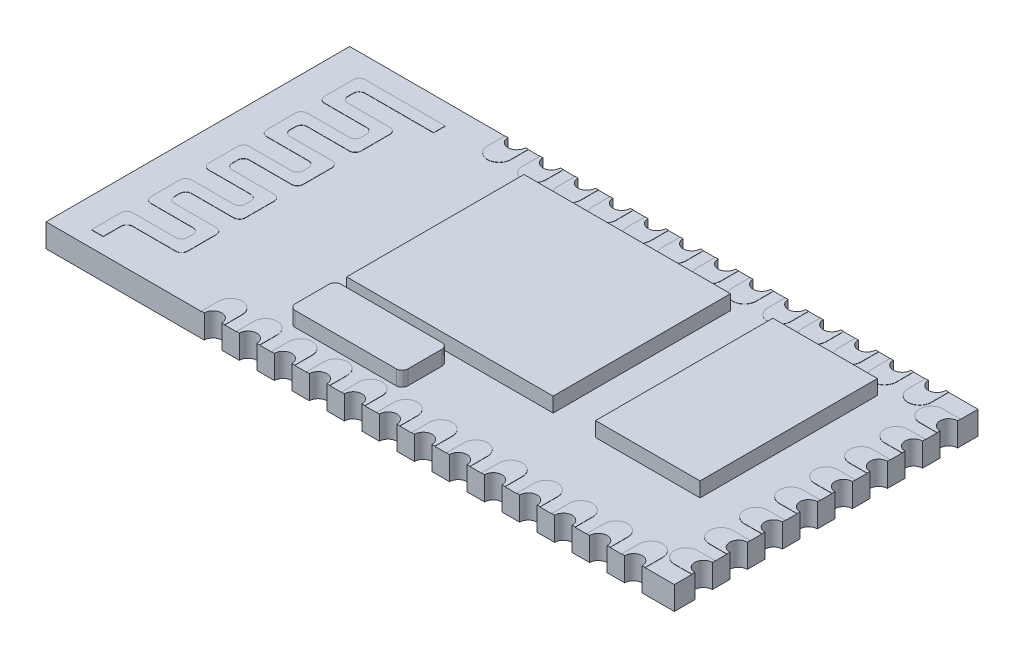
SolidWorks part; units mm, degrees
ref_plane "Front Plane" through (0, 0, 0) normal (0, 0, 1) x (1, 0, 0)
ref_plane "Top Plane" through (0, 0, 0) normal (0, 1, 0) x (1, 0, 0)
ref_plane "Right Plane" through (0, 0, 0) normal (1, 0, 0) x (0, 0, -1)
sketch "Sketch1" plane through (0, 0, 0) normal (0, 1, 0) x (1, 0, 0)
  line L1 (0, 0) -> (26.9, 0)
  line L2 (0, 0) -> (0, 13)
  line L3 (0, 13) -> (26.9, 13)
  line L4 (26.9, 0) -> (26.9, 13)
  dimension "D1" = 13
  dimension "D2" = 26.9
extrude "Boss-Extrude1" add sketch "Sketch1" along normal blind 1
sketch "Sketch2" plane through (0, 1, 0) normal (0, 1, 0) x (1, 0, 0)
  line L1 (24.2376, 11.3557) -> (19.7636, 11.3557)
  line L2 (24.2376, 11.3557) -> (24.2376, 3.7634)
  line L3 (24.2376, 3.7634) -> (19.7636, 3.7634)
  line L4 (19.7636, 11.3557) -> (19.7636, 3.7634)
  line L5 (9.1073, 11.3557) -> (17.9469, 11.3557)
  line L6 (9.1073, 11.3557) -> (9.1073, 3.7634)
  line L7 (9.1073, 3.7634) -> (17.9469, 3.7634)
  line L8 (17.9469, 11.3557) -> (17.9469, 3.7634)
extrude "Boss-Extrude2" add sketch "Sketch2" along normal blind 0.63
sketch "Sketch3" plane through (0, 1, 0) normal (0, 1, 0) x (1, 0, 0)
  line L0 (5.0017, 11.8414) -> (1.5699, 11.8414) construction
  line L1 (1.5699, 11.8414) -> (1.5699, 10.6027) construction
  line L2 (1.5699, 10.6027) -> (3.8747, 10.6027) construction
  line L3 (3.8747, 10.6027) -> (3.8747, 9.364) construction
  line L4 (3.8747, 9.364) -> (1.5699, 9.364) construction
  line L5 (1.5699, 9.364) -> (1.5699, 8.1252) construction
  line L6 (1.5699, 8.1252) -> (3.8747, 8.1252) construction
  line L7 (3.8747, 8.1252) -> (3.8747, 6.8865) construction
  line L8 (3.8747, 6.8865) -> (1.5699, 6.8865) construction
  line L9 (1.5699, 6.8865) -> (1.5699, 5.6478) construction
  line L10 (1.5699, 5.6478) -> (3.8747, 5.6478) construction
  line L11 (3.8747, 5.6478) -> (3.8747, 4.4091) construction
  line L12 (3.8747, 4.4091) -> (1.5699, 4.4091) construction
  line L13 (1.5699, 4.4091) -> (1.5699, 3.1704) construction
  line L14 (1.5699, 3.1704) -> (3.8747, 3.1704) construction
  line L15 (3.8747, 3.1704) -> (3.8747, 1.9317) construction
  line L16 (3.8747, 1.9317) -> (1.527, 1.9317) construction
  line L17 (1.527, 1.4451) -> (1.527, 0.1872) construction
  line L18 (5.0017, 12.0914) -> (1.5699, 12.0914)
  line L19 (1.3199, 11.8414) -> (1.3199, 10.6027)
  line L20 (1.5699, 10.3527) -> (3.3747, 10.3527)
  line L21 (3.6247, 10.1027) -> (3.6247, 9.864)
  line L22 (3.3747, 9.614) -> (1.5699, 9.614)
  line L23 (1.3199, 9.364) -> (1.3199, 8.1252)
  line L24 (1.5699, 7.8752) -> (3.3747, 7.8752)
  line L25 (3.6247, 7.6252) -> (3.6247, 7.3865)
  line L26 (3.3747, 7.1365) -> (1.5699, 7.1365)
  line L27 (1.3199, 6.8865) -> (1.3199, 5.6478)
  line L28 (1.5699, 5.3978) -> (3.3747, 5.3978)
  line L29 (3.6247, 5.1478) -> (3.6247, 4.9091)
  line L30 (3.3747, 4.6591) -> (1.5699, 4.6591)
  line L31 (1.3199, 4.4091) -> (1.3199, 3.1704)
  line L32 (1.5699, 2.9204) -> (3.3747, 2.9204)
  line L33 (3.6247, 2.6704) -> (3.6247, 2.4317)
  line L34 (3.3747, 2.1817) -> (1.527, 2.1817)
  line L35 (1.277, 1.9317) -> (1.277, 0.6739)
  line L36 (5.0017, 11.5914) -> (2.0699, 11.5914)
  line L37 (1.8199, 11.3414) -> (1.8199, 11.1027)
  line L38 (2.0699, 10.8527) -> (3.8747, 10.8527)
  line L39 (4.1247, 10.6027) -> (4.1247, 9.364)
  line L40 (3.8747, 9.114) -> (2.0699, 9.114)
  line L41 (1.8199, 8.864) -> (1.8199, 8.6252)
  line L42 (2.0699, 8.3752) -> (3.8747, 8.3752)
  line L43 (4.1247, 8.1252) -> (4.1247, 6.8865)
  line L44 (3.8747, 6.6365) -> (2.0699, 6.6365)
  line L45 (1.8199, 6.3865) -> (1.8199, 6.1478)
  line L46 (2.0699, 5.8978) -> (3.8747, 5.8978)
  line L47 (4.1247, 5.6478) -> (4.1247, 4.4091)
  line L48 (3.8747, 4.1591) -> (2.0699, 4.1591)
  line L49 (1.8199, 3.9091) -> (1.8199, 3.6704)
  line L50 (2.0699, 3.4204) -> (3.8747, 3.4204)
  line L51 (4.1247, 3.1704) -> (4.1247, 1.9317)
  line L52 (3.8747, 1.6817) -> (2.027, 1.6817)
  line L53 (1.777, 1.4317) -> (1.777, 0.6739)
  line L54 (5.0017, 12.0914) -> (5.0017, 11.5914)
  line L55 (1.777, 0.6739) -> (1.277, 0.6739)
  arc A0 (1.5699, 12.0914) -> (1.3199, 11.8414) centre (1.5699, 11.8414) ccw
  arc A1 (2.0699, 11.5914) -> (1.8199, 11.3414) centre (2.0699, 11.3414) ccw
  arc A2 (1.8199, 11.1027) -> (2.0699, 10.8527) centre (2.0699, 11.1027) ccw
  arc A3 (1.3199, 10.6027) -> (1.5699, 10.3527) centre (1.5699, 10.6027) ccw
  arc A4 (3.8747, 10.8527) -> (4.1247, 10.6027) centre (3.8747, 10.6027) cw
  arc A5 (3.3747, 10.3527) -> (3.6247, 10.1027) centre (3.3747, 10.1027) cw
  arc A6 (3.6247, 9.864) -> (3.3747, 9.614) centre (3.3747, 9.864) cw
  arc A7 (4.1247, 9.364) -> (3.8747, 9.114) centre (3.8747, 9.364) cw
  arc A8 (2.0699, 9.114) -> (1.8199, 8.864) centre (2.0699, 8.864) ccw
  arc A9 (1.5699, 9.614) -> (1.3199, 9.364) centre (1.5699, 9.364) ccw
  arc A10 (1.8199, 8.6252) -> (2.0699, 8.3752) centre (2.0699, 8.6252) ccw
  arc A11 (1.3199, 8.1252) -> (1.5699, 7.8752) centre (1.5699, 8.1252) ccw
  arc A12 (3.3747, 7.8752) -> (3.6247, 7.6252) centre (3.3747, 7.6252) cw
  arc A13 (3.8747, 8.3752) -> (4.1247, 8.1252) centre (3.8747, 8.1252) cw
  arc A14 (4.1247, 6.8865) -> (3.8747, 6.6365) centre (3.8747, 6.8865) cw
  arc A15 (3.6247, 7.3865) -> (3.3747, 7.1365) centre (3.3747, 7.3865) cw
  arc A16 (1.5699, 7.1365) -> (1.3199, 6.8865) centre (1.5699, 6.8865) ccw
  arc A17 (2.0699, 6.6365) -> (1.8199, 6.3865) centre (2.0699, 6.3865) ccw
  arc A18 (1.8199, 6.1478) -> (2.0699, 5.8978) centre (2.0699, 6.1478) ccw
  arc A19 (1.3199, 5.6478) -> (1.5699, 5.3978) centre (1.5699, 5.6478) ccw
  arc A20 (3.3747, 5.3978) -> (3.6247, 5.1478) centre (3.3747, 5.1478) cw
  arc A21 (3.8747, 5.8978) -> (4.1247, 5.6478) centre (3.8747, 5.6478) cw
  arc A22 (4.1247, 4.4091) -> (3.8747, 4.1591) centre (3.8747, 4.4091) cw
  arc A23 (3.6247, 4.9091) -> (3.3747, 4.6591) centre (3.3747, 4.9091) cw
  arc A24 (1.5699, 4.6591) -> (1.3199, 4.4091) centre (1.5699, 4.4091) ccw
  arc A25 (2.0699, 4.1591) -> (1.8199, 3.9091) centre (2.0699, 3.9091) ccw
  arc A26 (1.8199, 3.6704) -> (2.0699, 3.4204) centre (2.0699, 3.6704) ccw
  arc A27 (1.3199, 3.1704) -> (1.5699, 2.9204) centre (1.5699, 3.1704) ccw
  arc A28 (2.027, 1.6817) -> (1.777, 1.4317) centre (2.027, 1.4317) ccw
  arc A29 (1.527, 2.1817) -> (1.277, 1.9317) centre (1.527, 1.9317) ccw
  arc A30 (3.8747, 3.4204) -> (4.1247, 3.1704) centre (3.8747, 3.1704) cw
  arc A31 (3.3747, 2.9204) -> (3.6247, 2.6704) centre (3.3747, 2.6704) cw
  arc A32 (3.6247, 2.4317) -> (3.3747, 2.1817) centre (3.3747, 2.4317) cw
  arc A33 (4.1247, 1.9317) -> (3.8747, 1.6817) centre (3.8747, 1.9317) cw
  dimension "D1" = 0.25
extrude "Boss-Extrude3" add sketch "Sketch3" along normal blind 0.01
sketch "Sketch4" plane through (0, 1, 0) normal (0, 1, 0) x (1, 0, 0)
  line L1 (9.2531, 3.3678) -> (13.5796, 3.3678)
  line L2 (9.0031, 3.1178) -> (9.0031, 1.6655)
  line L3 (9.2531, 1.4155) -> (13.5796, 1.4155)
  line L4 (13.8296, 3.1178) -> (13.8296, 1.6655)
  arc A0 (13.5796, 1.4155) -> (13.8296, 1.6655) centre (13.5796, 1.6655) ccw
  arc A1 (9.2531, 3.3678) -> (9.0031, 3.1178) centre (9.2531, 3.1178) ccw
  arc A2 (9.0031, 1.6655) -> (9.2531, 1.4155) centre (9.2531, 1.6655) ccw
  arc A3 (13.5796, 3.3678) -> (13.8296, 3.1178) centre (13.5796, 3.1178) cw
  dimension "D1" = 0.25
extrude "Boss-Extrude4" add sketch "Sketch4" along normal up to surface (0.63 mm away) up to face at (13.5271, 1.63, -7.5596)
sketch "Sketch5" plane through (0, 1, 0) normal (0, 1, 0) x (1, 0, 0)
  line L0 (0, 6.5) -> (26.9, 6.5) construction
  line L1 (0, 13) -> (0, 0) construction
  line L2 (26.9, 0) -> (26.9, 13) construction
  line L3 (26.15, 11.75) -> (28.15, 11.75) construction
  line L4 (26.15, 12.25) -> (28.15, 12.25)
  line L5 (26.15, 11.25) -> (28.15, 11.25)
  line L7 (26.15, 10.25) -> (28.15, 10.25) construction
  line L8 (26.15, 10.75) -> (28.15, 10.75)
  line L9 (26.15, 9.75) -> (28.15, 9.75)
  line L10 (26.15, 8.75) -> (28.15, 8.75) construction
  line L11 (26.15, 9.25) -> (28.15, 9.25)
  line L12 (26.15, 8.25) -> (28.15, 8.25)
  line L13 (26.15, 7.25) -> (28.15, 7.25) construction
  line L14 (26.15, 7.75) -> (28.15, 7.75)
  line L15 (26.15, 6.75) -> (28.15, 6.75)
  line L16 (26.15, 5.75) -> (28.15, 5.75) construction
  line L17 (26.15, 6.25) -> (28.15, 6.25)
  line L18 (26.15, 5.25) -> (28.15, 5.25)
  line L19 (26.15, 4.25) -> (28.15, 4.25) construction
  line L20 (26.15, 4.75) -> (28.15, 4.75)
  line L21 (26.15, 3.75) -> (28.15, 3.75)
  line L22 (26.15, 2.75) -> (28.15, 2.75) construction
  line L23 (26.15, 3.25) -> (28.15, 3.25)
  line L24 (26.15, 2.25) -> (28.15, 2.25)
  line L25 (26.15, 1.25) -> (28.15, 1.25) construction
  line L26 (26.15, 1.75) -> (28.15, 1.75)
  line L27 (26.15, 0.75) -> (28.15, 0.75)
  line L30 (25.15, 12.25) -> (25.15, 14.25) construction
  line L31 (24.65, 12.25) -> (24.65, 14.25)
  line L32 (25.65, 12.25) -> (25.65, 14.25)
  line L33 (26.9, 13) -> (0, 13) construction
  line L34 (23.65, 12.25) -> (23.65, 14.25) construction
  line L35 (23.15, 12.25) -> (23.15, 14.25)
  line L36 (24.15, 12.25) -> (24.15, 14.25)
  line L37 (22.15, 12.25) -> (22.15, 14.25) construction
  line L38 (21.65, 12.25) -> (21.65, 14.25)
  line L39 (22.65, 12.25) -> (22.65, 14.25)
  line L40 (20.65, 12.25) -> (20.65, 14.25) construction
  line L41 (20.15, 12.25) -> (20.15, 14.25)
  line L42 (21.15, 12.25) -> (21.15, 14.25)
  line L43 (19.15, 12.25) -> (19.15, 14.25) construction
  line L44 (18.65, 12.25) -> (18.65, 14.25)
  line L45 (19.65, 12.25) -> (19.65, 14.25)
  line L46 (17.65, 12.25) -> (17.65, 14.25) construction
  line L47 (17.15, 12.25) -> (17.15, 14.25)
  line L48 (18.15, 12.25) -> (18.15, 14.25)
  line L49 (16.15, 12.25) -> (16.15, 14.25) construction
  line L50 (15.65, 12.25) -> (15.65, 14.25)
  line L51 (16.65, 12.25) -> (16.65, 14.25)
  line L52 (14.65, 12.25) -> (14.65, 14.25) construction
  line L53 (14.15, 12.25) -> (14.15, 14.25)
  line L54 (15.15, 12.25) -> (15.15, 14.25)
  line L55 (13.15, 12.25) -> (13.15, 14.25) construction
  line L56 (12.65, 12.25) -> (12.65, 14.25)
  line L57 (13.65, 12.25) -> (13.65, 14.25)
  line L58 (11.65, 12.25) -> (11.65, 14.25) construction
  line L59 (11.15, 12.25) -> (11.15, 14.25)
  line L60 (12.15, 12.25) -> (12.15, 14.25)
  line L61 (10.15, 12.25) -> (10.15, 14.25) construction
  line L62 (9.65, 12.25) -> (9.65, 14.25)
  line L63 (10.65, 12.25) -> (10.65, 14.25)
  line L64 (8.65, 12.25) -> (8.65, 14.25) construction
  line L65 (8.15, 12.25) -> (8.15, 14.25)
  line L66 (9.15, 12.25) -> (9.15, 14.25)
  line L67 (7.15, 12.25) -> (7.15, 14.25) construction
  line L68 (6.65, 12.25) -> (6.65, 14.25)
  line L69 (7.65, 12.25) -> (7.65, 14.25)
  line L70 (25.15, 0.75) -> (25.15, -1.25) construction
  line L71 (24.65, 0.75) -> (24.65, -1.25)
  line L72 (25.65, 0.75) -> (25.65, -1.25)
  line L73 (23.65, 0.75) -> (23.65, -1.25) construction
  line L74 (23.15, 0.75) -> (23.15, -1.25)
  line L75 (24.15, 0.75) -> (24.15, -1.25)
  line L76 (22.15, 0.75) -> (22.15, -1.25) construction
  line L77 (21.65, 0.75) -> (21.65, -1.25)
  line L78 (22.65, 0.75) -> (22.65, -1.25)
  line L79 (20.65, 0.75) -> (20.65, -1.25) construction
  line L80 (20.15, 0.75) -> (20.15, -1.25)
  line L81 (21.15, 0.75) -> (21.15, -1.25)
  line L82 (19.15, 0.75) -> (19.15, -1.25) construction
  line L83 (18.65, 0.75) -> (18.65, -1.25)
  line L84 (19.65, 0.75) -> (19.65, -1.25)
  line L85 (17.65, 0.75) -> (17.65, -1.25) construction
  line L86 (17.15, 0.75) -> (17.15, -1.25)
  line L87 (18.15, 0.75) -> (18.15, -1.25)
  line L88 (16.15, 0.75) -> (16.15, -1.25) construction
  line L89 (15.65, 0.75) -> (15.65, -1.25)
  line L90 (16.65, 0.75) -> (16.65, -1.25)
  line L91 (14.65, 0.75) -> (14.65, -1.25) construction
  line L92 (14.15, 0.75) -> (14.15, -1.25)
  line L93 (15.15, 0.75) -> (15.15, -1.25)
  line L94 (13.15, 0.75) -> (13.15, -1.25) construction
  line L95 (12.65, 0.75) -> (12.65, -1.25)
  line L96 (13.65, 0.75) -> (13.65, -1.25)
  line L97 (11.65, 0.75) -> (11.65, -1.25) construction
  line L98 (11.15, 0.75) -> (11.15, -1.25)
  line L99 (12.15, 0.75) -> (12.15, -1.25)
  line L100 (10.15, 0.75) -> (10.15, -1.25) construction
  line L101 (9.65, 0.75) -> (9.65, -1.25)
  line L102 (10.65, 0.75) -> (10.65, -1.25)
  line L103 (8.65, 0.75) -> (8.65, -1.25) construction
  line L104 (8.15, 0.75) -> (8.15, -1.25)
  line L105 (9.15, 0.75) -> (9.15, -1.25)
  line L106 (7.15, 0.75) -> (7.15, -1.25) construction
  line L107 (6.65, 0.75) -> (6.65, -1.25)
  line L108 (7.65, 0.75) -> (7.65, -1.25)
  arc A0 (26.15, 12.25) -> (26.15, 11.25) centre (26.15, 11.75) ccw
  arc A1 (28.15, 11.25) -> (28.15, 12.25) centre (28.15, 11.75) ccw
  arc A2 (26.15, 10.75) -> (26.15, 9.75) centre (26.15, 10.25) ccw
  arc A3 (28.15, 9.75) -> (28.15, 10.75) centre (28.15, 10.25) ccw
  arc A4 (26.15, 9.25) -> (26.15, 8.25) centre (26.15, 8.75) ccw
  arc A5 (28.15, 8.25) -> (28.15, 9.25) centre (28.15, 8.75) ccw
  arc A6 (26.15, 7.75) -> (26.15, 6.75) centre (26.15, 7.25) ccw
  arc A7 (28.15, 6.75) -> (28.15, 7.75) centre (28.15, 7.25) ccw
  arc A8 (26.15, 6.25) -> (26.15, 5.25) centre (26.15, 5.75) ccw
  arc A9 (28.15, 5.25) -> (28.15, 6.25) centre (28.15, 5.75) ccw
  arc A10 (26.15, 4.75) -> (26.15, 3.75) centre (26.15, 4.25) ccw
  arc A11 (28.15, 3.75) -> (28.15, 4.75) centre (28.15, 4.25) ccw
  arc A12 (26.15, 3.25) -> (26.15, 2.25) centre (26.15, 2.75) ccw
  arc A13 (28.15, 2.25) -> (28.15, 3.25) centre (28.15, 2.75) ccw
  arc A14 (26.15, 1.75) -> (26.15, 0.75) centre (26.15, 1.25) ccw
  arc A15 (28.15, 0.75) -> (28.15, 1.75) centre (28.15, 1.25) ccw
  arc A16 (24.65, 12.25) -> (25.65, 12.25) centre (25.15, 12.25) ccw
  arc A17 (25.65, 14.25) -> (24.65, 14.25) centre (25.15, 14.25) ccw
  arc A18 (23.15, 12.25) -> (24.15, 12.25) centre (23.65, 12.25) ccw
  arc A19 (24.15, 14.25) -> (23.15, 14.25) centre (23.65, 14.25) ccw
  arc A20 (21.65, 12.25) -> (22.65, 12.25) centre (22.15, 12.25) ccw
  arc A21 (22.65, 14.25) -> (21.65, 14.25) centre (22.15, 14.25) ccw
  arc A22 (20.15, 12.25) -> (21.15, 12.25) centre (20.65, 12.25) ccw
  arc A23 (21.15, 14.25) -> (20.15, 14.25) centre (20.65, 14.25) ccw
  arc A24 (18.65, 12.25) -> (19.65, 12.25) centre (19.15, 12.25) ccw
  arc A25 (19.65, 14.25) -> (18.65, 14.25) centre (19.15, 14.25) ccw
  arc A26 (17.15, 12.25) -> (18.15, 12.25) centre (17.65, 12.25) ccw
  arc A27 (18.15, 14.25) -> (17.15, 14.25) centre (17.65, 14.25) ccw
  arc A28 (15.65, 12.25) -> (16.65, 12.25) centre (16.15, 12.25) ccw
  arc A29 (16.65, 14.25) -> (15.65, 14.25) centre (16.15, 14.25) ccw
  arc A30 (14.15, 12.25) -> (15.15, 12.25) centre (14.65, 12.25) ccw
  arc A31 (15.15, 14.25) -> (14.15, 14.25) centre (14.65, 14.25) ccw
  arc A32 (12.65, 12.25) -> (13.65, 12.25) centre (13.15, 12.25) ccw
  arc A33 (13.65, 14.25) -> (12.65, 14.25) centre (13.15, 14.25) ccw
  arc A34 (11.15, 12.25) -> (12.15, 12.25) centre (11.65, 12.25) ccw
  arc A35 (12.15, 14.25) -> (11.15, 14.25) centre (11.65, 14.25) ccw
  arc A36 (9.65, 12.25) -> (10.65, 12.25) centre (10.15, 12.25) ccw
  arc A37 (10.65, 14.25) -> (9.65, 14.25) centre (10.15, 14.25) ccw
  arc A38 (8.15, 12.25) -> (9.15, 12.25) centre (8.65, 12.25) ccw
  arc A39 (9.15, 14.25) -> (8.15, 14.25) centre (8.65, 14.25) ccw
  arc A40 (6.65, 12.25) -> (7.65, 12.25) centre (7.15, 12.25) ccw
  arc A41 (7.65, 14.25) -> (6.65, 14.25) centre (7.15, 14.25) ccw
  arc A42 (24.65, 0.75) -> (25.65, 0.75) centre (25.15, 0.75) cw
  arc A43 (25.65, -1.25) -> (24.65, -1.25) centre (25.15, -1.25) cw
  arc A44 (23.15, 0.75) -> (24.15, 0.75) centre (23.65, 0.75) cw
  arc A45 (24.15, -1.25) -> (23.15, -1.25) centre (23.65, -1.25) cw
  arc A46 (21.65, 0.75) -> (22.65, 0.75) centre (22.15, 0.75) cw
  arc A47 (22.65, -1.25) -> (21.65, -1.25) centre (22.15, -1.25) cw
  arc A48 (20.15, 0.75) -> (21.15, 0.75) centre (20.65, 0.75) cw
  arc A49 (21.15, -1.25) -> (20.15, -1.25) centre (20.65, -1.25) cw
  arc A50 (18.65, 0.75) -> (19.65, 0.75) centre (19.15, 0.75) cw
  arc A51 (19.65, -1.25) -> (18.65, -1.25) centre (19.15, -1.25) cw
  arc A52 (17.15, 0.75) -> (18.15, 0.75) centre (17.65, 0.75) cw
  arc A53 (18.15, -1.25) -> (17.15, -1.25) centre (17.65, -1.25) cw
  arc A54 (15.65, 0.75) -> (16.65, 0.75) centre (16.15, 0.75) cw
  arc A55 (16.65, -1.25) -> (15.65, -1.25) centre (16.15, -1.25) cw
  arc A56 (14.15, 0.75) -> (15.15, 0.75) centre (14.65, 0.75) cw
  arc A57 (15.15, -1.25) -> (14.15, -1.25) centre (14.65, -1.25) cw
  arc A58 (12.65, 0.75) -> (13.65, 0.75) centre (13.15, 0.75) cw
  arc A59 (13.65, -1.25) -> (12.65, -1.25) centre (13.15, -1.25) cw
  arc A60 (11.15, 0.75) -> (12.15, 0.75) centre (11.65, 0.75) cw
  arc A61 (12.15, -1.25) -> (11.15, -1.25) centre (11.65, -1.25) cw
  arc A62 (9.65, 0.75) -> (10.65, 0.75) centre (10.15, 0.75) cw
  arc A63 (10.65, -1.25) -> (9.65, -1.25) centre (10.15, -1.25) cw
  arc A64 (8.15, 0.75) -> (9.15, 0.75) centre (8.65, 0.75) cw
  arc A65 (9.15, -1.25) -> (8.15, -1.25) centre (8.65, -1.25) cw
  arc A66 (6.65, 0.75) -> (7.65, 0.75) centre (7.15, 0.75) cw
  arc A67 (7.65, -1.25) -> (6.65, -1.25) centre (7.15, -1.25) cw
  point P8 (27.15, 11.75)
  point P18 (27.15, 10.25)
  point P25 (27.15, 8.75)
  point P32 (27.15, 7.25)
  point P39 (27.15, 5.75)
  point P46 (27.15, 4.25)
  point P53 (27.15, 2.75)
  point P60 (27.15, 1.25)
  point P66 (25.15, 13.25)
  point P75 (23.65, 13.25)
  point P82 (22.15, 13.25)
  point P89 (20.65, 13.25)
  point P96 (19.15, 13.25)
  point P103 (17.65, 13.25)
  point P110 (16.15, 13.25)
  point P117 (14.65, 13.25)
  point P124 (13.15, 13.25)
  point P131 (11.65, 13.25)
  point P138 (10.15, 13.25)
  point P145 (8.65, 13.25)
  point P152 (7.15, 13.25)
  point P157 (25.15, -0.25)
  point P164 (23.65, -0.25)
  point P171 (22.15, -0.25)
  point P178 (20.65, -0.25)
  point P185 (19.15, -0.25)
  point P192 (17.65, -0.25)
  point P199 (16.15, -0.25)
  point P206 (14.65, -0.25)
  point P213 (13.15, -0.25)
  point P220 (11.65, -0.25)
  point P227 (10.15, -0.25)
  point P234 (8.65, -0.25)
  point P241 (7.15, -0.25)
  dimension "D4" = 0.75
  dimension "D1" = 1
  dimension "D2" = 1.25
  dimension "D3" = 2
  dimension "D6" = 2
  dimension "D7" = 1
  dimension "D8" = 0.75
  dimension "D9" = 1.75
  dimension "D5" = 8
  dimension "D10" = 13
extrude "Boss-Extrude5" add sketch "Sketch5" along normal blind 0.01
sketch "Sketch7" plane through (0, 1.01, 0) normal (0, 1, 0) x (1, 0, 0)
  line L1 (6.65, 13) -> (26.9, 13)
  line L2 (6.65, 13) -> (6.65, 15.0045)
  line L3 (6.65, 15.0045) -> (26.9, 15.0045)
  line L5 (26.9, 15.0045) -> (29.0707, 15.0045)
  line L6 (26.9, 15.0045) -> (26.9, 0)
  line L8 (29.0707, 15.0045) -> (29.0707, 0)
  line L9 (29.0707, 0) -> (6.65, 0)
  line L10 (29.0707, 0) -> (29.0707, -1.8715)
  line L11 (29.0707, -1.8715) -> (6.65, -1.8715)
  line L12 (6.65, 0) -> (6.65, -1.8715)
  line M2 (7.65, 12.25) -> (7.65, 14.25)
  arc M3 (7.65, 14.25) -> (6.65, 14.25) centre (7.15, 14.25) ccw
  line M4 (6.65, 14.25) -> (6.65, 12.25)
extrude "Cut-Extrude1" cut sketch "Sketch7" against normal through all contours L6 L3 L2 L1 M3 M2 | L9 L8 L5 L6 | L1 M4 M2 M3 | L9 L12 L11 L10
sketch "Sketch8" plane through (0, 1.01, 0) normal (0, 1, 0) x (1, 0, 0)
  line L0 (6.65, 13) -> (7.65, 13) construction
  line L1 (6.65, 0) -> (7.65, 0) construction
  circle A0 centre (7.15, 13) radius 0.375
  circle A1 centre (7.15, 0) radius 0.375
  dimension "D1" = 0.75
  dimension "D2" = 0.75
extrude "Cut-Extrude2" cut sketch "Sketch8" against normal through all
pattern_linear "LPattern1" count 13 spacing 1.5 along (1, 0, 0) of "Cut-Extrude2"
sketch "Sketch9" plane through (0, 1.01, 0) normal (0, 1, 0) x (1, 0, 0)
  line L0 (26.9, 12.25) -> (26.9, 11.25) construction
  circle A0 centre (26.9, 11.75) radius 0.375
  dimension "D1" = 0.75
extrude "Cut-Extrude3" cut sketch "Sketch9" against normal through all
pattern_linear "LPattern2" count 8 spacing 1.5 along (0, 0, 1) of "Cut-Extrude3"
